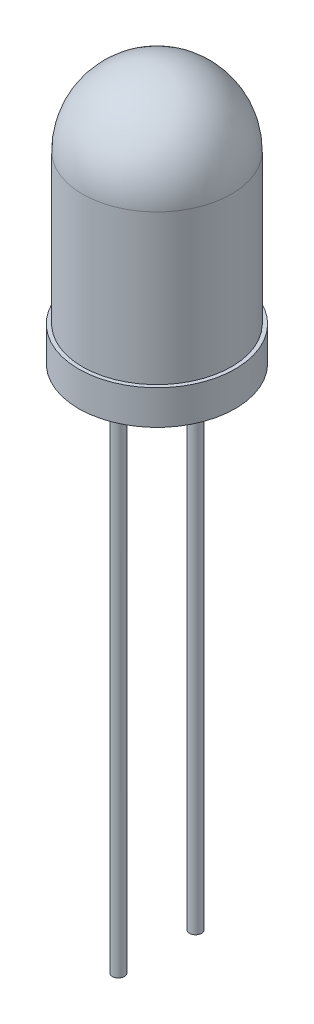
SolidWorks part; units mm, degrees
ref_plane "Front Plane" through (0, 0, 0) normal (0, 0, 1) x (1, 0, 0)
ref_plane "Top Plane" through (0, 0, 0) normal (0, 1, 0) x (1, 0, 0)
ref_plane "Right Plane" through (0, 0, 0) normal (1, 0, 0) x (0, 0, -1)
sketch "Sketch1" plane through (0, 0, 0) normal (0, 1, 0) x (1, 0, 0)
  circle A0 centre (0, 0) radius 2.575
  dimension "D1" = 5.15
extrude "Boss-Extrude1" add sketch "Sketch1" along normal blind 8.5 contours A0
sketch "Sketch2" plane through (0, 8.5, 0) normal (0, 1, 0) x (1, 0, 0)
  circle A0 centre (0, 0) radius 2.45
  circle A1 centre (0, 0) radius 2.575
  dimension "D1" = 4.9
  dimension "D2" = 5.15
extrude "Cut-Extrude1" cut sketch "Sketch2" against normal blind 7.37
fillet "Fillet2" radius 2.45 1 edges at (0, 8.5, 2.45)
sketch "Sketch4" plane through (0, 0, 0) normal (0, -1, 0) x (-1, 0, 0)
  line L0 (2.575, 0) -> (-2.575, 0) construction
  circle A0 centre (0, 0) radius 2.575 construction
  circle A1 centre (1.27, 0) radius 0.2
  circle A2 centre (-1.27, 0) radius 0.2
  dimension "D1" = 0.4
  dimension "D2" = 0.4
  dimension "D3" = 1.27
  dimension "D4" = 1.27
extrude "Boss-Extrude4" add sketch "Sketch4" along normal blind 18
sketch "Sketch6" plane through (0, -18, 0) normal (0, -1, 0) x (1, 0, 0)
  circle A0 centre (1.27, 0) radius 0.225
  dimension "D1" = 0.45
extrude "Cut-Extrude2" cut sketch "Sketch6" against normal blind 2.5
equation "\"D1@Cut-Extrude1\"=8.5-1.13"
